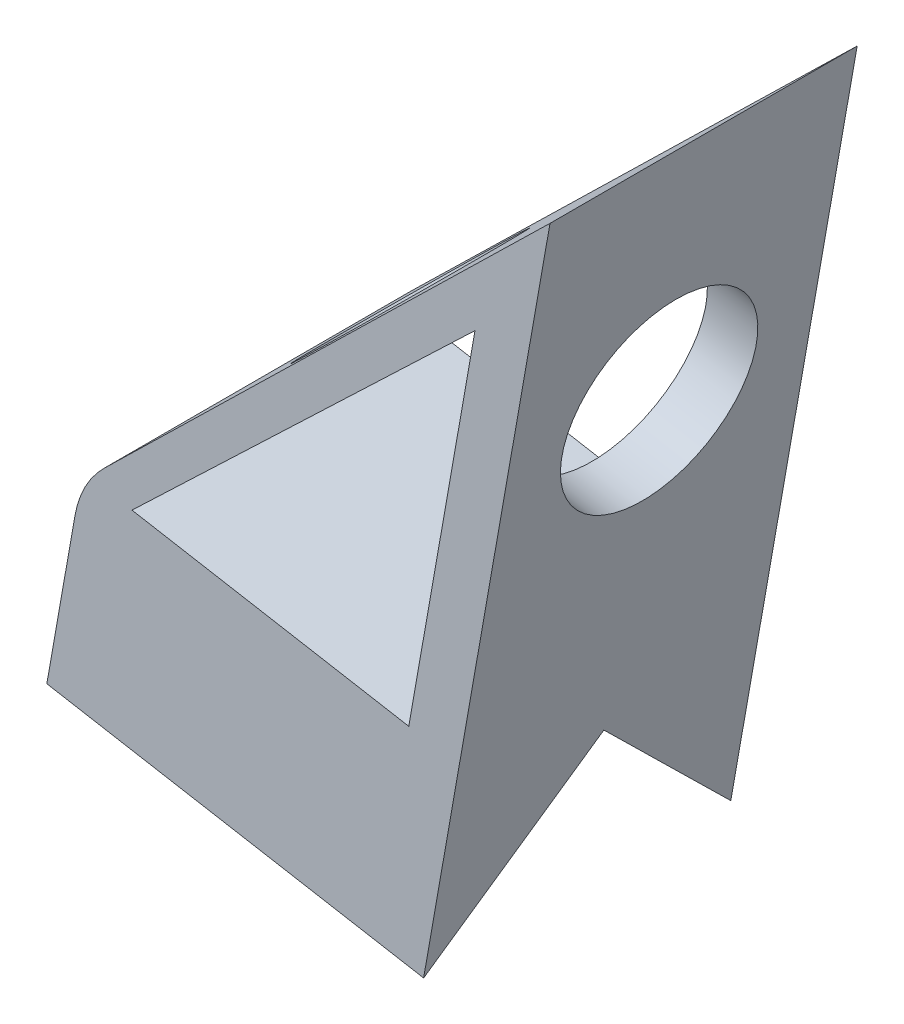
SolidWorks part; units mm, degrees
material "Plain Carbon Steel"
ref_plane "Front Plane" through (0, 0, 0) normal (0, 0, 1) x (1, 0, 0)
ref_plane "Top Plane" through (0, 0, 0) normal (0, 1, 0) x (1, 0, 0)
ref_plane "Right Plane" through (0, 0, 0) normal (1, 0, 0) x (0, 0, -1)
sketch "Sketch2" plane through (0, 0, 0) normal (0, 0, 1) x (1, 0, 0)
  line L0 (0, 0) -> (0, 203.2) construction
  line L4 (0, 203.2) -> (-31.3509, 25.4)
  line L5 (-31.3509, 25.4) -> (-159.1464, 47.9338)
  line L6 (0, 0) -> (-237.4515, 0) construction
  line L7 (0, 203.2) -> (-159.1464, 47.9338)
  dimension "D1" = 203.2
  dimension "D2" = 10
  dimension "D3" = 10
extrude "Boss-Extrude1" add sketch "Sketch2" against normal blind 76.2
sketch "Sketch6" plane through (0, 0, 0) normal (0, 0, 1) x (1, 0, 0)
  line L1 (0, 203.2) -> (-159.1464, 47.9338) construction
  line L6 (-18.5982, 170.861) -> (8.9634, 173.0056) construction
  line L7 (-18.5982, 170.861) -> (-35.0367, 77.6336)
  line L10 (-31.3509, 25.4) -> (0, 203.2) construction
  line L13 (-35.0367, 77.6336) -> (-103.6992, 89.7406)
  line L15 (-18.5982, 170.861) -> (-103.6992, 89.7406)
  line L16 (-159.1464, 47.9338) -> (-31.3509, 25.4) construction
  dimension "D1" = 36.372
  dimension "D4" = 50.8
  dimension "D5" = 10.16
  dimension "D6" = 12.7
extrude "Cut-Extrude3" cut sketch "Sketch6" against normal through all
sketch "Sketch8" plane through (0, 0, 0) normal (0, 0, 1) x (1, 0, 0)
  line L0 (-124.8198, 41.8811) -> (-116.3988, 89.6392)
  line L1 (-159.1464, 47.9338) -> (-31.3509, 25.4) construction
  line L2 (0, 203.2) -> (-159.1464, 47.9338) construction
  line L3 (-116.3988, 89.6392) -> (-159.1464, 47.9338)
  line L4 (-159.1464, 47.9338) -> (-124.8198, 41.8811)
  dimension "D2" = 12.7
extrude "Cut-Extrude4" cut sketch "Sketch8" against normal through all
sketch "Sketch9" plane through (-128.2182, 22.6083, 0) normal (-0.9848, 0.1736, 0) x (0, 0, 1)
  line L0 (-76.2, 19.5701) -> (-38.1, 57.6701)
  line L1 (-38.1, 57.6701) -> (0, 19.5701)
  line L2 (0, 19.5701) -> (-76.2, 19.5701)
  line L3 (-38.1, 19.5701) -> (-38.1, 62.9767) construction
  dimension "D1" = 90
  dimension "D2" = 0
extrude "Cut-Extrude5" cut sketch "Sketch9" against normal through all
sketch "Sketch10" plane through (-101.5691, 104.1073, 0) normal (-0.6983, 0.7158, 0) x (0.7158, 0.6983, 0)
  line L0 (-20.7184, 76.2) -> (-20.7184, 0) construction
  circle A0 centre (40.2416, 38.1) radius 24.13
  dimension "D1" = 48.26
  dimension "D2" = 60.96
extrude "Slanted Circle" cut sketch "Sketch10" against normal up to next
sketch "Sketch11" plane through (-34.7492, 6.1272, 0) normal (0.9848, -0.1736, 0) x (0, 0, -1)
  line L0 (76.2, 200.1129) -> (0, 200.1129) construction
  circle A0 centre (38.1, 136.6129) radius 24.13
  dimension "D1" = 48.26
  dimension "D2" = 63.5
extrude "Back Circle Cut" cut sketch "Sketch11" against normal up to next
fillet "Fillet2" radius 25.4 1 edges at (-116.3988, 89.6392, -38.1)
